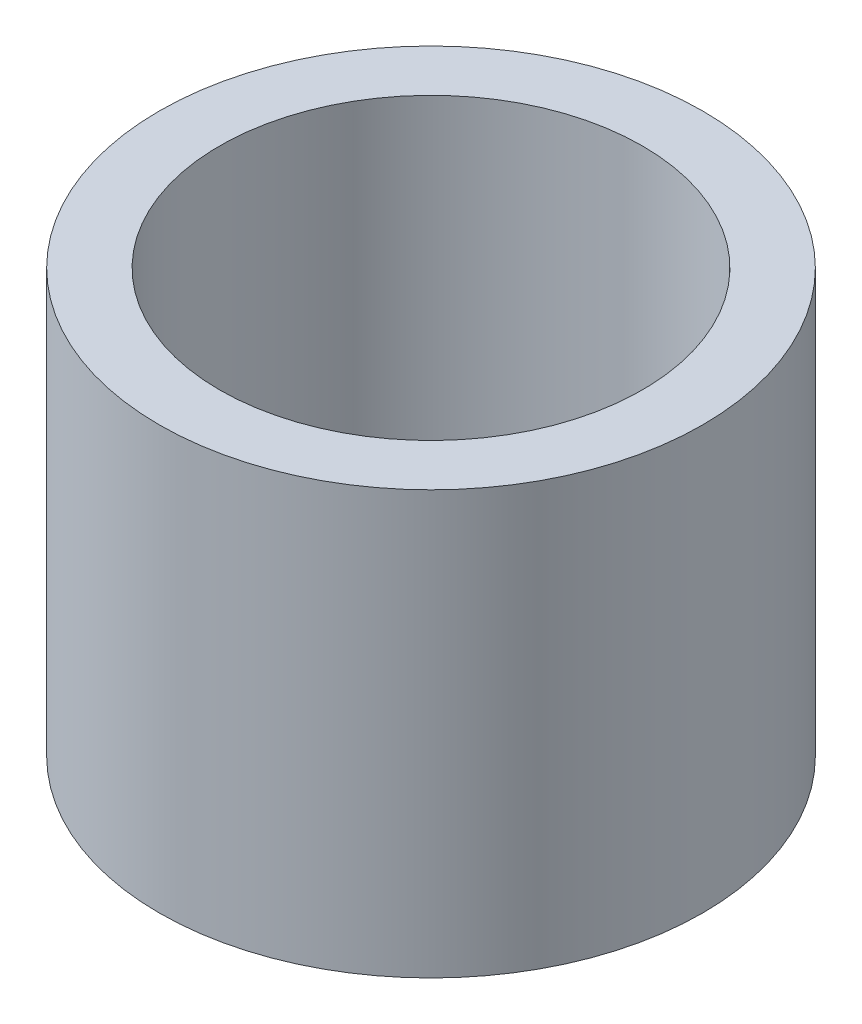
SolidWorks part; units mm, degrees
ref_plane "前视基准面" through (0, 0, 0) normal (0, 0, 1) x (1, 0, 0)
ref_plane "上视基准面" through (0, 0, 0) normal (0, 1, 0) x (1, 0, 0)
ref_plane "右视基准面" through (0, 0, 0) normal (1, 0, 0) x (0, 0, -1)
sketch "草图1" plane through (0, 0, 0) normal (0, 1, 0) x (1, 0, 0)
  circle A0 centre (0, 0) radius 4.5
  circle A1 centre (0, 0) radius 3.5
  dimension "D1" = 7
  dimension "D2" = 9
extrude "凸台-拉伸1" add sketch "草图1" along normal blind 7
